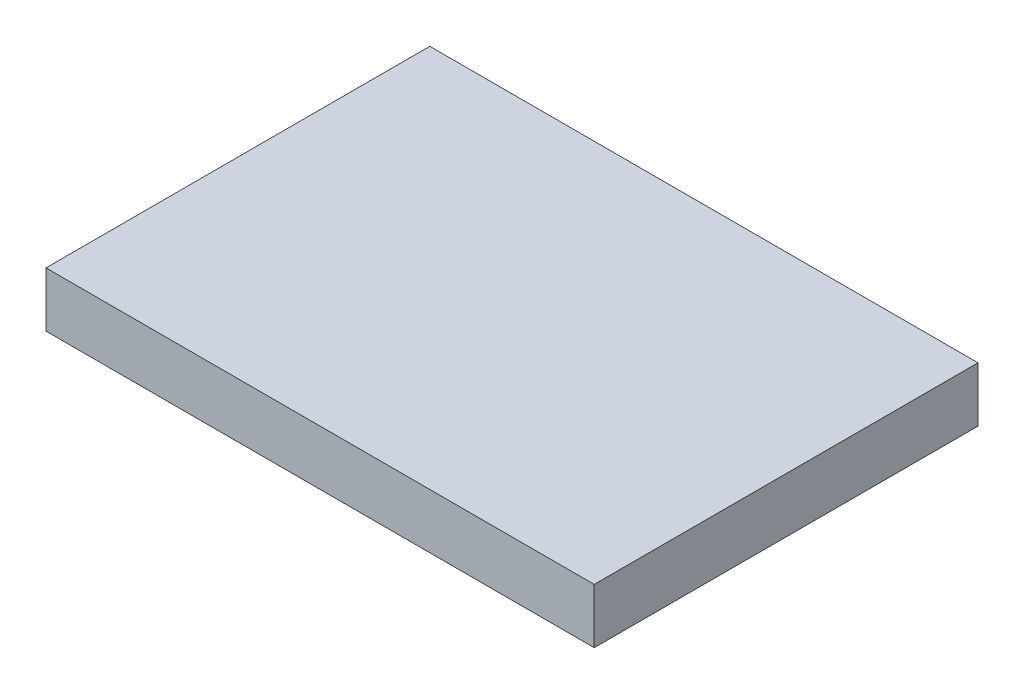
SolidWorks part; units mm, degrees
ref_plane "Спереди" through (0, 0, 0) normal (0, 0, 1) x (1, 0, 0)
ref_plane "Сверху" through (0, 0, 0) normal (0, 1, 0) x (1, 0, 0)
ref_plane "Справа" through (0, 0, 0) normal (1, 0, 0) x (0, 0, -1)
other "Configuration Table"
sketch "Эскиз1" plane through (0, 0, 0) normal (0, 1, 0) x (1, 0, 0)
  line L1 (50, -35) -> (-50, -35)
  line L2 (50, -35) -> (50, 35)
  line L3 (50, 35) -> (-50, 35)
  line L4 (-50, -35) -> (-50, 35)
  line L5 (50, -35) -> (-50, 35) construction
  line L6 (50, 35) -> (-50, -35) construction
  point P0 (0, 0)
  dimension "D1" = 70
  dimension "D2" = 100
extrude "Бобышка-Вытянуть1" add sketch "Эскиз1" along normal blind 10
